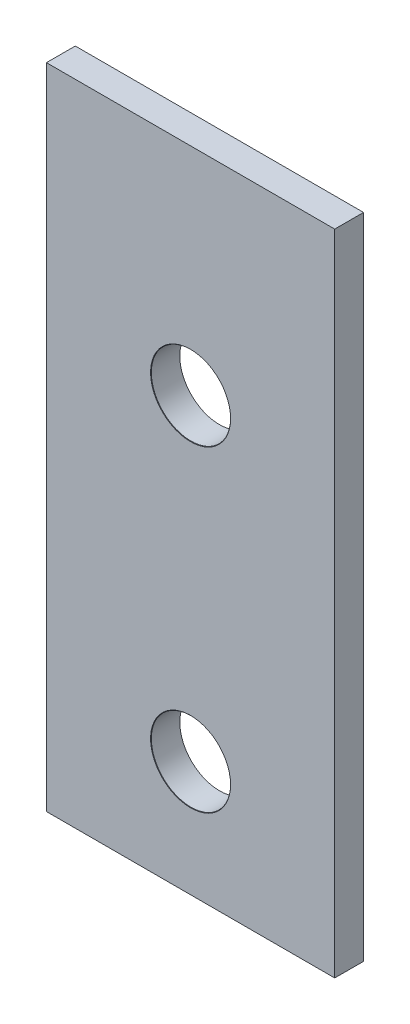
SolidWorks part; units mm, degrees
ref_plane "Front Plane" through (0, 0, 0) normal (0, 0, 1) x (1, 0, 0)
ref_plane "Top Plane" through (0, 0, 0) normal (0, 1, 0) x (1, 0, 0)
ref_plane "Right Plane" through (0, 0, 0) normal (1, 0, 0) x (0, 0, -1)
sketch "Sketch1" plane through (0, 0, 0) normal (0, 0, 1) x (1, 0, 0)
  line L1 (0, 0) -> (20, 0)
  line L2 (0, 0) -> (0, 45)
  line L3 (0, 45) -> (20, 45)
  line L4 (20, 0) -> (20, 45)
  line L5 (10, 45) -> (10, 0) construction
  line L6 (0, 22.5) -> (20, 22.5) construction
  point P68 (10, 22.5)
  dimension "D1" = 20
  dimension "D2" = 45
extrude "Boss-Extrude1" add sketch "Sketch1" along normal blind 2
hole_wizard "M5 Clearance Hole1" positions "Sketch2" profile "Sketch3" hole size "M5" standard "ANSI Metric" end condition through all
sketch "Sketch2" plane through (0, 0, 2) normal (0, 0, 1) x (1, 0, 0)
  line L0 (10, 30) -> (10, 8) construction
  line L2 (10, 8) -> (10, 0) construction
  line L3 (0, 0) -> (20, 0) construction
  point P0 (10, 30)
  point P2 (10, 8)
  dimension "D1" = 22
  dimension "D2" = 8
sketch "Sketch3" plane through (10, 30, 2) normal (1, 0, 0) x (0, -1, 0)
  line L0 (0, 0) -> (0, 2)
  line L1 (0, 2) -> (2.75, 2)
  line L2 (2.75, 2) -> (2.75, 0.025)
  line L3 (2.75, 0.025) -> (2.775, 0)
  line L5 (2.775, 0) -> (0, 0)
  line L6 (-2.75, 0.025) -> (-2.775, 0) construction
  line L11 (0, -6.35) -> (0, 107.95) construction
  dimension "Thru Hole Dia." = 5.5
  dimension "Thru Hole Depth" = 2
  dimension "Near C'Sink Dia." = 5.55
  dimension "Near C'Sink Angle" = 90
sketch "Sketch4" plane through (0, 0, 0) normal (0, 0, -1) x (-1, 0, 0)
  line L1 (-20, 0) -> (0, 0)
  line L2 (-20, 0) -> (-20, 20)
  line L3 (-20, 20) -> (0, 20)
  line L4 (0, 0) -> (0, 20)
  line L5 (-10, 20) -> (-10, 0) construction
  line L6 (-20, 10) -> (0, 10) construction
  circle A0 centre (-10, 30) radius 2.75 construction
  point P72 (-10, 10)
  dimension "D1" = 10
extrude "Cut-Extrude1" [suppressed] cut sketch "Sketch4" against normal blind 2
sketch "Sketch5" [suppressed] plane through (0, 0, 0) normal (1, 0, 0) x (0, 0, -1)
  line L0 (0, 0) -> (0, 15)
  line L1 (0, 15) -> (3.5, 15)
  line L2 (3.5, 15) -> (3.5, 27)
  line L3 (3.5, 27) -> (-2, 27)
  line L4 (-2, 27) -> (-2, 0)
  line L5 (55, 0) -> (-55, 0) construction
  line L6 (-2, 0) -> (0, 0)
  dimension "D1" = 15
  dimension "D2" = 2
  dimension "D3" = 3.5
  dimension "D4" = 12
extrude "Boss-Extrude2" [suppressed] add sketch "Sketch5" along normal blind 20 separate body
sketch "Sketch6" [suppressed] plane through (0, 0, -3.5) normal (0, 0, -1) x (-1, 0, 0)
  line L0 (-10, 15) -> (-10, 17.75) construction
  line L1 (-20, 15) -> (0, 15) construction
  line L2 (-12.75, 15) -> (-12.75, 17.75)
  line L3 (-7.25, 15) -> (-7.25, 17.75)
  arc A0 (-12.75, 15) -> (-7.25, 15) centre (-10, 15) ccw
  arc A1 (-7.25, 17.75) -> (-12.75, 17.75) centre (-10, 17.75) ccw
  arc A2 (-12.75, 17.75) -> (-7.25, 17.75) centre (-10, 17.75) ccw construction
  point P4 (-10, 16.375)
  dimension "D1" = 5.5
extrude "Cut-Extrude2" [suppressed] cut sketch "Sketch6" against normal blind 20
